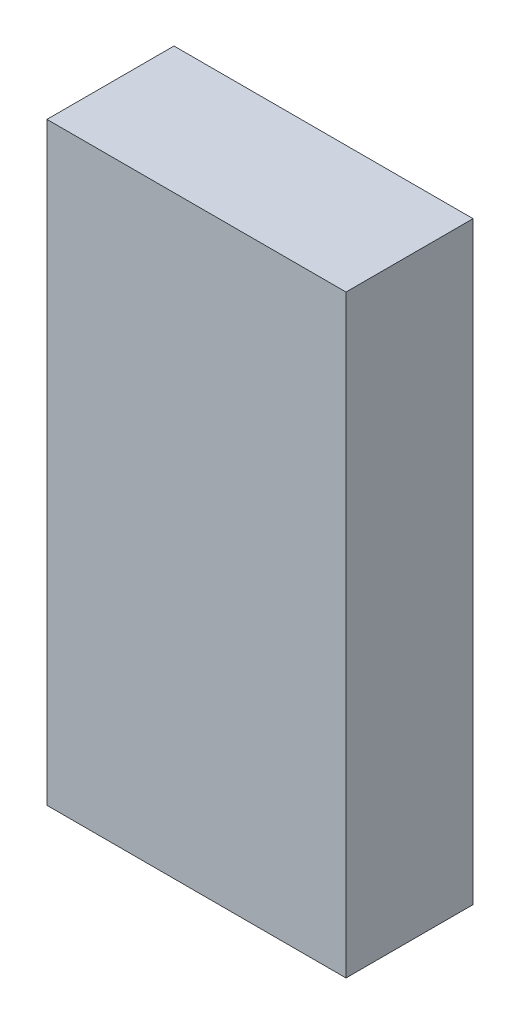
SolidWorks part; units mm, degrees
ref_plane "Front Plane" through (0, 0, 0) normal (0, 0, 1) x (1, 0, 0)
ref_plane "Top Plane" through (0, 0, 0) normal (0, 1, 0) x (1, 0, 0)
ref_plane "Right Plane" through (0, 0, 0) normal (1, 0, 0) x (0, 0, -1)
sketch "Sketch1" plane through (0, 0, 0) normal (0, 1, 0) x (1, 0, 0)
  line L1 (-12.2555, -5.207) -> (12.2555, -5.207)
  line L2 (-12.2555, -5.207) -> (-12.2555, 5.207)
  line L3 (-12.2555, 5.207) -> (12.2555, 5.207)
  line L4 (12.2555, -5.207) -> (12.2555, 5.207)
  line L5 (-12.2555, -5.207) -> (12.2555, 5.207) construction
  line L6 (-12.2555, 5.207) -> (12.2555, -5.207) construction
  point P0 (0, 0)
  dimension "D1" = 10.414
  dimension "D2" = 24.511
extrude "Boss-Extrude1" add sketch "Sketch1" along normal blind 48.6918
